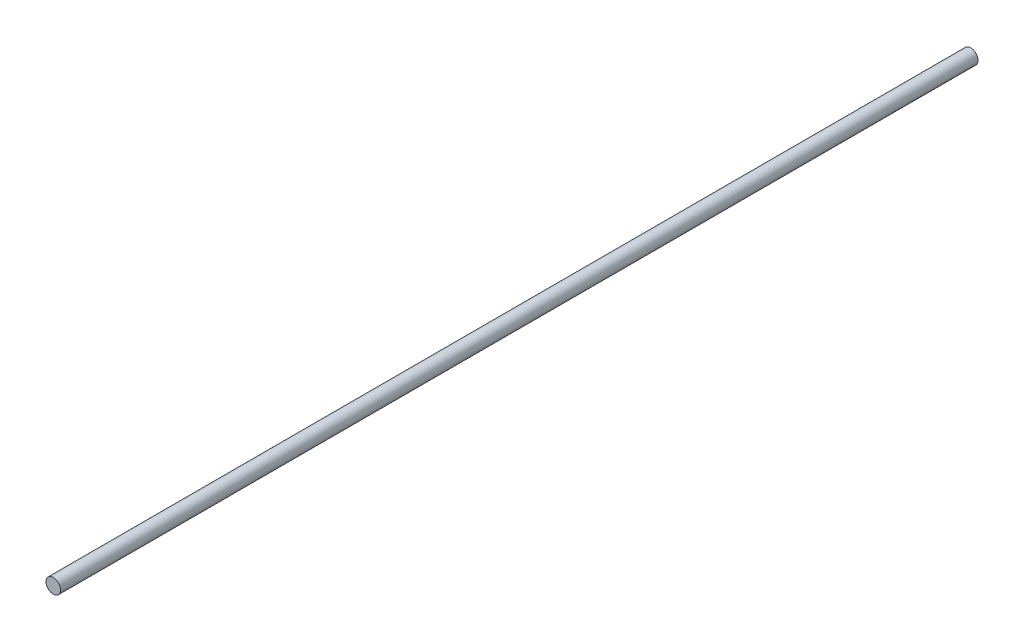
SolidWorks part; units mm, degrees
ref_plane "Alzado" through (0, 0, 0) normal (0, 0, 1) x (1, 0, 0)
ref_plane "Planta" through (0, 0, 0) normal (0, 1, 0) x (1, 0, 0)
ref_plane "Vista lateral" through (0, 0, 0) normal (1, 0, 0) x (0, 0, -1)
sketch "Croquis1" plane through (0, 0, 0) normal (0, 0, 1) x (1, 0, 0)
  circle A0 centre (0, 0) radius 6.35
  dimension "D1" = 12.7
sketch "Croquis2" plane through (0, 0, 0) normal (1, 0, 0) x (0, 0, -1)
  line L0 (0, 0) -> (800, 0)
  dimension "D1" = 800
sweep "Barrer1" add profiles "Croquis1" path "Croquis2"
